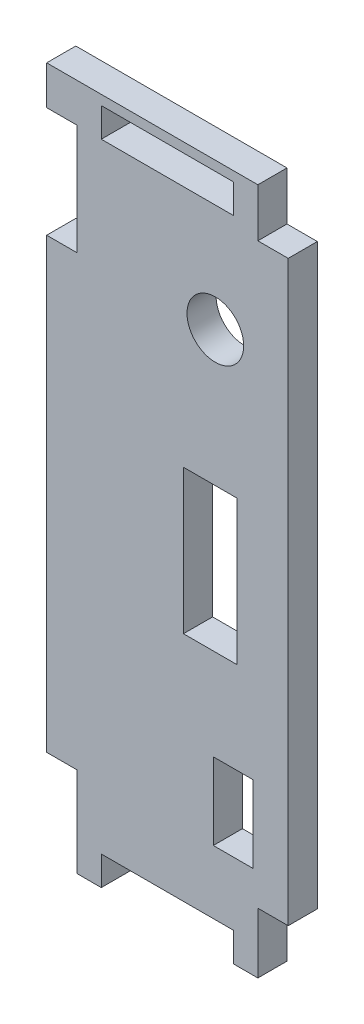
SolidWorks part; units mm, degrees
ref_plane "Front Plane" through (0, 0, 0) normal (0, 0, 1) x (1, 0, 0)
ref_plane "Top Plane" through (0, 0, 0) normal (0, 1, 0) x (1, 0, 0)
ref_plane "Right Plane" through (0, 0, 0) normal (1, 0, 0) x (0, 0, -1)
sketch "Sketch1" plane through (0, 0, 0) normal (0, 0, 1) x (1, 0, 0)
  line L0 (3.175, 53.213) -> (0, 53.213) construction
  line L1 (3.175, 6.35) -> (0, 6.35) construction
  line L2 (3.175, 53.213) -> (0, 53.213)
  line L3 (3.175, 6.35) -> (0, 6.35)
  line L4 (0, 53.213) -> (0, 6.35)
  line L5 (3.175, 6.35) -> (3.175, -1.8034)
  line L6 (3.175, -1.8034) -> (22.098, -1.8034)
  line L7 (22.098, -1.8034) -> (22.098, 3.2766)
  line L8 (22.098, 3.2766) -> (25.273, 3.2766)
  line L9 (25.273, 3.2766) -> (25.273, 63.754)
  line L10 (25.273, 63.754) -> (22.098, 63.754)
  line L11 (22.098, 63.754) -> (22.098, 68.834)
  line L12 (22.098, 68.834) -> (3.175, 68.834)
  line L13 (3.175, 68.834) -> (3.175, 53.213)
  line L14 (3.175, 64.77) -> (0, 64.77) construction
  line L15 (5.715, -1.8034) -> (5.715, 0)
  line L16 (5.715, 64.77) -> (19.558, 64.77)
  line L17 (5.715, 64.77) -> (5.715, 67.818)
  line L18 (5.715, 67.818) -> (19.558, 67.818)
  line L19 (19.558, 64.77) -> (19.558, 67.818)
  line L20 (5.715, 0) -> (19.558, 0)
  line L21 (19.558, 0) -> (19.558, -1.8034)
  line L22 (3.175, 68.834) -> (0, 68.834)
  line L23 (0, 68.834) -> (0, 64.77)
  line L24 (0, 64.77) -> (3.175, 64.77)
  line L25 (3.175, -1.8034) -> (3.175, -3.048)
  line L26 (3.175, -3.048) -> (3.175, -1.8034)
  line L27 (5.715, -1.8034) -> (5.715, -3.048)
  line L28 (5.715, -3.048) -> (3.175, -3.048)
  line L29 (22.098, -1.8034) -> (22.098, -3.048)
  line L30 (22.098, -3.048) -> (19.558, -3.048)
  line L31 (19.558, -3.048) -> (19.558, -1.8034)
  line B0 (21.6154, 6.6294) -> (21.6154, 14.6685)
  line B1 (19.9009, 24.257) -> (19.9009, 39.3446)
  line B2 (17.4371, 14.6685) -> (21.6154, 14.6685)
  line B3 (17.4371, 6.6294) -> (17.4371, 14.6685)
  line B4 (17.4371, 6.6294) -> (21.6154, 6.6294)
  line B5 (19.9009, 24.257) -> (14.3129, 24.257)
  line B6 (14.3129, 24.257) -> (14.3129, 39.3446)
  line B7 (19.9009, 39.3446) -> (14.3129, 39.3446)
  line B8 (22.098, 46.863) -> (22.098, 84.963)
  line B9 (10.7188, 0) -> (17.018, 0)
  circle B10 centre (17.6467, 53.4861) radius 2.9655
  dimension "D1" = 18.923
  dimension "D2" = 5.08
  dimension "D3" = 5.08
  dimension "D4" = 4.064
  dimension "D5" = 3.048
  dimension "D6" = 2.54
  dimension "D7" = 2.54
  dimension "D8" = 2.54
  dimension "D9" = 2.54
  dimension "D10" = 1.2446
sketch_block_instance "RPIHolePlacement-1"
sketch_block "RPIHolePlacement"
extrude "Boss-Extrude1" add sketch "Sketch1" along normal blind 3.048
